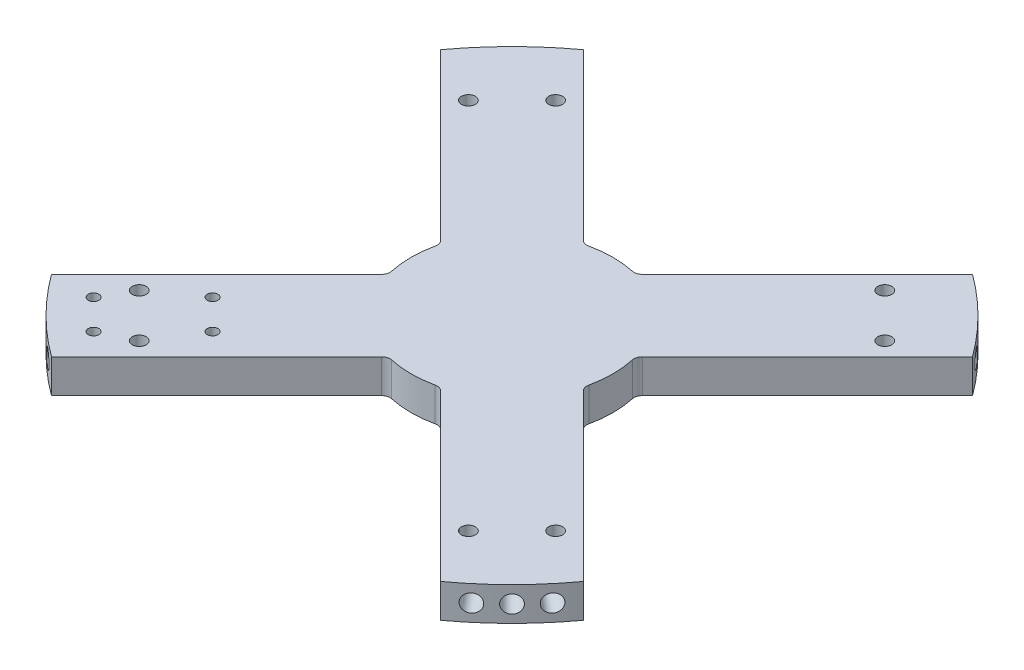
SolidWorks part; units mm, degrees
other "DetailItem1"
other "DetailItem2"
other "DetailItem3"
other "DetailItem4"
other "DetailItem5"
other "DetailItem6"
other "DetailItem7"
other "DetailItem8"
other "Weld Folder"
material "6061-T6 (SS)"
ref_plane "Front Plane" through (0, 0, 0) normal (0, 0, 1) x (1, 0, 0)
ref_plane "Top Plane" through (0, 0, 0) normal (0, 1, 0) x (1, 0, 0)
ref_plane "Right Plane" through (0, 0, 0) normal (1, 0, 0) x (0, 0, -1)
sketch "Sketch5" plane through (0, 0, 0) normal (0, 1, 0) x (1, 0, 0)
  line L48 (-0.0346, 0.0346) -> (0.0346, -0.0346) construction
  line L53 (0, 0) -> (-103.2729, -103.2729) construction
  line L55 (-19.2429, 19.2429) -> (19.2429, -19.2429) construction
  line L56 (-11.8332, -44.1621) -> (-88.1081, -120.437)
  line L58 (-44.1621, -11.8332) -> (-120.437, -88.1081)
  line L59 (-49.9706, -82.2996) -> (-82.2996, -49.9706) construction
  line L60 (-44.1621, 11.8332) -> (-120.437, 88.1081)
  line L61 (-11.8332, 44.1621) -> (-88.1081, 120.437)
  line L62 (11.8332, 44.1621) -> (88.1081, 120.437)
  line L63 (44.1621, 11.8332) -> (120.437, 88.1081)
  line L64 (44.1621, -11.8332) -> (120.437, -88.1081)
  line L65 (11.8332, -44.1621) -> (88.1081, -120.437)
  line L66 (-88.1081, 120.437) -> (0, 0) construction
  line L67 (0, 0) -> (-120.437, 88.1081) construction
  arc A0 (-88.1081, -120.437) -> (-120.437, -88.1081) centre (0, 0) cw
  arc A1 (-44.1621, 11.8332) -> (-44.1621, -11.8332) centre (0, 0) ccw
  arc A2 (11.8332, 44.1621) -> (-11.8332, 44.1621) centre (0, 0) ccw
  arc A3 (-120.437, 88.1081) -> (-88.1081, 120.437) centre (0, 0) cw
  arc A4 (44.1621, -11.8332) -> (44.1621, 11.8332) centre (0, 0) ccw
  arc A5 (88.1081, 120.437) -> (120.437, 88.1081) centre (0, 0) cw
  arc A6 (-11.8332, -44.1621) -> (11.8332, -44.1621) centre (0, 0) ccw
  arc A7 (120.437, -88.1081) -> (88.1081, -120.437) centre (0, 0) cw
  point P32 (0, 0)
  dimension "D3" = 149.225
  dimension "D5" = 45.72
  dimension "D1" = 90
  dimension "D2" = 146.05
  dimension "D4" = 45.72
  dimension "D6" = 4
extrude "Boss-Extrude3" add sketch "Sketch5" along normal blind 15.24
sketch "Sketch6" plane through (0, 15.24, 0) normal (0, 1, 0) x (1, 0, 0)
  line L0 (0, 0) -> (-84.4144, -84.4144) construction
  line L1 (-84.4144, -84.4144) -> (-74.5361, -94.2927) construction
  line L3 (0, 174.0525) -> (0, -174.0525) construction
  line L4 (0, 0) -> (102.9231, 0) construction
  circle A27 centre (-74.5361, -94.2927) radius 3.175
  circle A46 centre (-94.2927, -74.5361) radius 3.175
  circle A64 centre (94.2927, -74.5361) radius 3.175
  circle A65 centre (74.5361, -94.2927) radius 3.175
  circle A66 centre (94.2927, 74.5361) radius 3.175
  circle A67 centre (74.5361, 94.2927) radius 3.175
  circle A68 centre (-94.2927, 74.5361) radius 3.175
  circle A69 centre (-74.5361, 94.2927) radius 3.175
  point P23 (0, 0)
  point P24 (0, 0)
  dimension "D2" = 6.35
  dimension "D1" = 13.97
  dimension "D3" = 119.38
  dimension "D4" = 45
extrude "Cut-Extrude2" cut sketch "Sketch6" against normal through all
sketch "Sketch46" plane through (0, 0, 0) normal (0, -1, 0) x (1, 0, 0)
  line L0 (-77.7111, 94.2927) -> (-94.2927, 77.7111)
  line L1 (-94.2927, 77.7111) -> (-91.1177, 74.5361)
  line L2 (-91.1177, 74.5361) -> (-74.5361, 91.1177)
  line L3 (-74.5361, 91.1177) -> (-77.7111, 94.2927)
  line L5 (82.1374, 74.5361) -> (65.5559, 91.1177)
  line L6 (85.3124, 77.7111) -> (82.1374, 74.5361)
  line L7 (68.7309, 94.2927) -> (85.3124, 77.7111)
  line L8 (65.5559, 91.1177) -> (68.7309, 94.2927)
  line L10 (85.3124, -68.7309) -> (82.1374, -65.5559)
  line L11 (68.7309, -85.3124) -> (85.3124, -68.7309)
  line L12 (65.5559, -82.1374) -> (68.7309, -85.3124)
  line L13 (82.1374, -65.5559) -> (65.5559, -82.1374)
  line L14 (-91.1177, -65.5559) -> (-74.5361, -82.1374)
  line L15 (-94.2927, -68.7309) -> (-91.1177, -65.5559)
  line L16 (-77.7111, -85.3124) -> (-94.2927, -68.7309)
  line L17 (-74.5361, -82.1374) -> (-77.7111, -85.3124)
  circle A0 centre (-74.5361, 94.2927) radius 3.175 construction
  circle A1 centre (-94.2927, 74.5361) radius 3.175 construction
split line "Split Line4"
sketch "Sketch53" plane through (0, 15.24, 0) normal (0, 1, 0) x (1, 0, 0)
  line L1 (-44.1621, -11.8332) -> (-120.437, -88.1081) construction
  line L2 (11.8332, -44.1621) -> (88.1081, -120.437) construction
  line L3 (-120.437, 88.1081) -> (-44.1621, 11.8332) construction
  circle A0 centre (-88.4555, -101.0279) radius 2.413
  circle A1 centre (-61.5148, -74.0871) radius 2.413
  circle A2 centre (-101.9259, -87.5575) radius 2.413
  circle A3 centre (-74.9851, -60.6167) radius 2.413
  dimension "D7" = 4.826
  dimension "D1" = 19.05
  dimension "D2" = 19.05
  dimension "D3" = 38.1
  dimension "D4" = 12.7
  dimension "D5" = 12.7
  dimension "D6" = 38.1
  dimension "D8" = 73.025
  dimension "D9" = 73.025
extrude "Cut-Extrude6" cut sketch "Sketch53" against normal up to next contours A0 | A1 | A3 | A2
sketch "Sketch56" plane through (0, 15.24, 0) normal (0, 1, 0) x (1, 0, 0)
  line L0 (0, 0) -> (85.7157, 102.152) construction
  line L1 (0, 0) -> (-176.5821, 0) construction
  line L2 (0, 0) -> (-165.1308, -165.1308) construction
  line L3 (0, 0) -> (102.152, 85.7157) construction
  dimension "D1" = 5
  dimension "D2" = 45
ref_plane "Plane1" through (-95.92, 0, 114.313) normal (-0.6428, 0, 0.766) x (0.766, 0, 0.6428)
ref_plane "Plane2" through (-114.313, 0, 95.92) normal (-0.766, 0, 0.6428) x (0.6428, 0, 0.766)
sketch "Sketch55" plane through (-95.92, 0, 114.313) normal (-0.6428, 0, 0.766) x (0.766, 0, 0.6428)
  line L0 (0, 7.62) -> (0, 0) construction
  line L1 (0, 7.62) -> (0, 15.24) construction
  line L2 (-34729.6355, 15.24) -> (34752.7915, 15.24) construction
  circle A0 centre (0, 7.62) radius 3.9688
  dimension "D1" = 7.9375
fillet "Fillet1" radius 3.81 8 edges at (-11.8332, 7.62, 44.1621) (11.8332, 7.62, 44.1621) (-44.1621, 7.62, 11.8332) (-44.1621, 7.62, -11.8332) (-11.8332, 7.62, -44.1621) (11.8332, 7.62, -44.1621) (44.1621, 7.62, -11.8332) (44.1621, 7.62, 11.8332)
sketch "Sketch57" plane through (-114.313, 0, 95.92) normal (-0.766, 0, 0.6428) x (0.6428, 0, 0.766)
  line L0 (-19.1354, 7.62) -> (35.6253, 7.62) construction
  line L1 (-19.1354, 15.24) -> (-19.1354, 0) construction
  line L2 (35.6253, 15.24) -> (35.6253, 0) construction
  line L3 (0, 0) -> (0, 15.24) construction
  line L4 (34729.6355, 15.24) -> (-34752.7915, 15.24) construction
  circle A1 centre (0, 7.62) radius 3.9688
  dimension "D1" = 7.9375
extrude "Cut-Extrude8" cut sketch "Sketch57" against normal blind 12.7
extrude "Cut-Extrude9" cut sketch "Sketch55" against normal blind 12.7
pattern_circular "CirPattern2" count 4 over 360 about axis through (0, 0, 0) along (0, 1, 0) of "Cut-Extrude9", "Cut-Extrude8"
ref_plane "Plane3" through (-105.518, 0, 105.518) normal (-0.7071, 0, 0.7071) x (0.7071, 0, 0.7071)
sketch "Sketch58" plane through (-105.518, 0, 105.518) normal (-0.7071, 0, 0.7071) x (0.7071, 0, 0.7071)
  line L0 (0, 0) -> (0, 15.24) construction
  line L1 (17431.1485, 15.24) -> (-17442.7708, 15.24) construction
  circle A0 centre (0, 7.62) radius 3.9688
  dimension "D1" = 7.9375
extrude "Cut-Extrude10" cut sketch "Sketch58" against normal blind 12.7
pattern_circular "CirPattern3" count 4 over 360 about axis through (0, 0, 0) along (0, 1, 0) of "Cut-Extrude10"
equation "\"Rocket Diameter\"= 12"
equation "\"Rocket Thickness\"= .25"
equation "\"Plate_Mount\"= \"Rocket Diameter\" - 6 * \"Rocket Thickness\""
equation "\"Beam_Thickness\"= \"Rocket Diameter\" / 20"
equation "\"Cord Diameter\"=0.25"
equation "\"Center_Circle\"= \"Rocket Diameter\" / 12"
equation "\"D1@Sketch6\"=\"Beam_Thickness\"/2+\"Cord Diameter\""
equation "\"D2@Sketch6\"=\"Cord Diameter\""
equation "\"D3@Sketch6\"= \"Inner Radius\" * 4 / 5"
equation "\"Shear Pin Distance\"= 2"
equation "\"D2@Sketch5\"=(\"Rocket Diameter\"/2)-\"Rocket Thickness\""
equation "\"D3@Sketch5\"= \"Inner Radius\""
equation "\"D4@Sketch5\"=\"Beam_Thickness\"*3"
equation "\"D5@Sketch5\"=\"Beam_Thickness\"*3"
equation "\"Center Radius\"= ( \"Beam_Thickness\" * 4 * .75 + .25 * ( \"Plate_Mount\" / 2 ) ) / 2"
equation "\"Inner Radius\"= ( \"Rocket Diameter\" - \"Rocket Thickness\" ) * 0.5"
